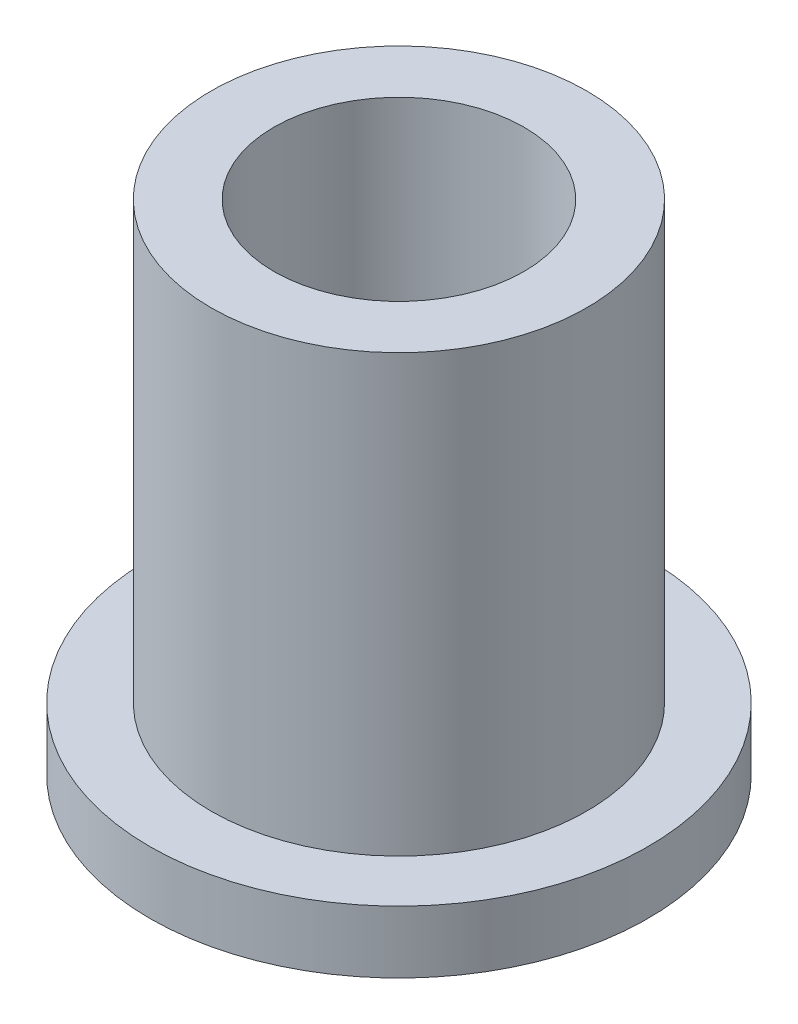
SolidWorks part; units mm, degrees
ref_plane "Front" through (0, 0, 0) normal (0, 0, 1) x (1, 0, 0)
ref_plane "Top" through (0, 0, 0) normal (0, 1, 0) x (1, 0, 0)
ref_plane "Right" through (0, 0, 0) normal (1, 0, 0) x (0, 0, -1)
sketch "Sketch1" plane through (0, 0, 0) normal (0, 1, 0) x (1, 0, 0)
  circle A0 centre (0, 0) radius 3.1877
  circle A1 centre (0, 0) radius 4.7879
  circle A2 centre (0, 0) radius 6.35
  dimension "ID" = 6.3754
  dimension "OD" = 9.5758
  dimension "FlangeOD" = 12.7
sketch "Sketch2" plane through (0, 0, 0) normal (0, 1, 0) x (1, 0, 0)
  circle A0 centre (0, 0) radius 3.1877 construction
  circle A1 centre (0, 0) radius 4.7879 construction
  circle A2 centre (0, 0) radius 3.1877
  circle A3 centre (0, 0) radius 4.7879
extrude "Boss-Extrude1" add sketch "Sketch2" along normal blind 12.7
sketch "Sketch3" plane through (0, 0, 0) normal (0, 1, 0) x (1, 0, 0)
  circle A0 centre (0, 0) radius 6.35 construction
  circle A1 centre (0, 0) radius 4.7879 construction
  circle A2 centre (0, 0) radius 6.35
  circle A3 centre (0, 0) radius 4.7879
extrude "Boss-Extrude2" add sketch "Sketch3" along normal blind 1.5875
